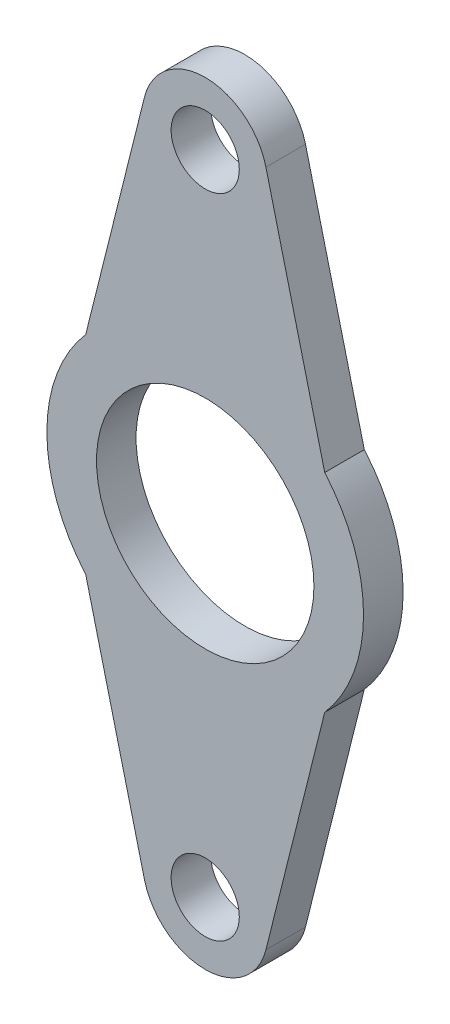
SolidWorks part; units mm, degrees
ref_plane "Front Plane" through (0, 0, 0) normal (0, 0, 1) x (1, 0, 0)
ref_plane "Top Plane" through (0, 0, 0) normal (0, 1, 0) x (1, 0, 0)
ref_plane "Right Plane" through (0, 0, 0) normal (1, 0, 0) x (0, 0, -1)
sketch "Sketch1" plane through (0, 0, 0) normal (0, 0, 1) x (1, 0, 0)
  line L0 (9.7409, 54.3696) -> (19.1721, 16.661)
  line L1 (-9.7409, 54.3696) -> (-19.1721, 16.661)
  line L2 (0, 0) -> (71.0753, 0) construction
  line L3 (9.7409, -54.3696) -> (19.1721, -16.661)
  line L4 (-9.7409, -54.3696) -> (-19.1721, -16.661)
  circle A0 centre (0, 0) radius 17.442
  circle A1 centre (0, 0) radius 25.4
  circle A2 centre (0, 51.9333) radius 10.0409
  circle A3 centre (0, -51.9333) radius 10.0409
  circle A4 centre (0, 51.9333) radius 5.4689
  circle A5 centre (0, 51.9333) radius 4.9609 construction
  circle A6 centre (0, 51.9333) radius 4.9609 construction
  circle A7 centre (0, -51.9333) radius 5.4689
  dimension "D1" = 5.08
  dimension "D2" = 50.8
  dimension "D3" = 0.508
extrude "Boss-Extrude1" add sketch "Sketch1" along normal blind 6.35 contours A2 L1 A1 L0 | A2 | A1 A0 | A3 L3 A1 L4 | A3
